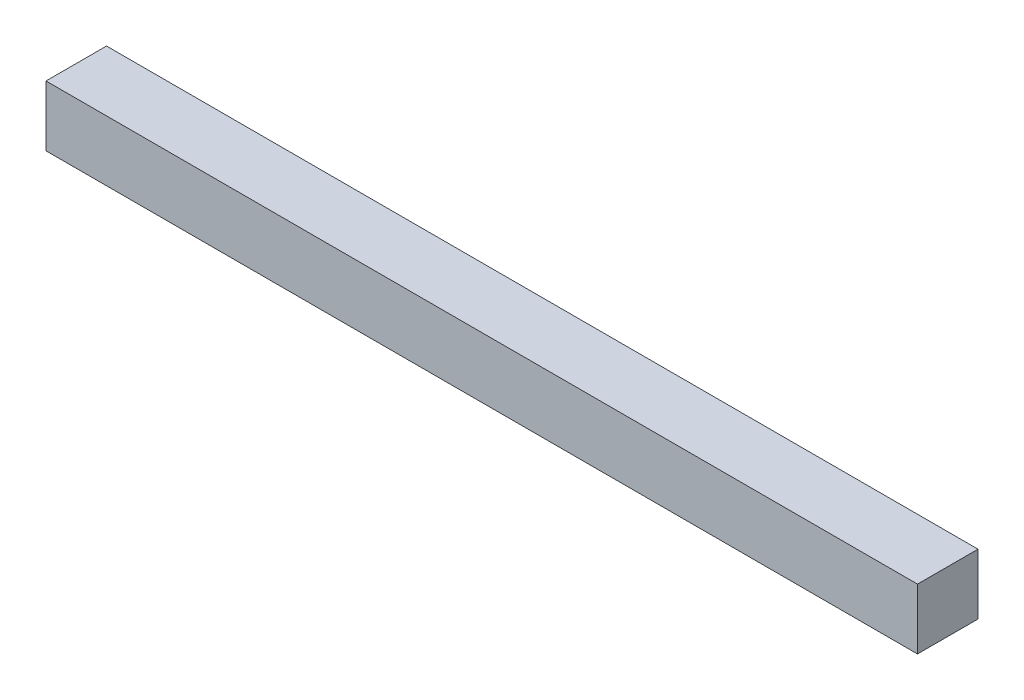
SolidWorks part; units mm, degrees
ref_plane "Front Plane" through (0, 0, 0) normal (0, 0, 1) x (1, 0, 0)
ref_plane "Top Plane" through (0, 0, 0) normal (0, 1, 0) x (1, 0, 0)
ref_plane "Right Plane" through (0, 0, 0) normal (1, 0, 0) x (0, 0, -1)
sketch "Sketch1" plane through (0, 0, 0) normal (0, 1, 0) x (1, 0, 0)
  line L1 (0, 0) -> (365.76, 0)
  line L2 (0, 0) -> (0, 25.4)
  line L3 (0, 25.4) -> (365.76, 25.4)
  line L4 (365.76, 0) -> (365.76, 25.4)
  dimension "D1" = 365.76
  dimension "D2" = 25.4
extrude "Boss-Extrude1" add sketch "Sketch1" along normal blind 25.4
